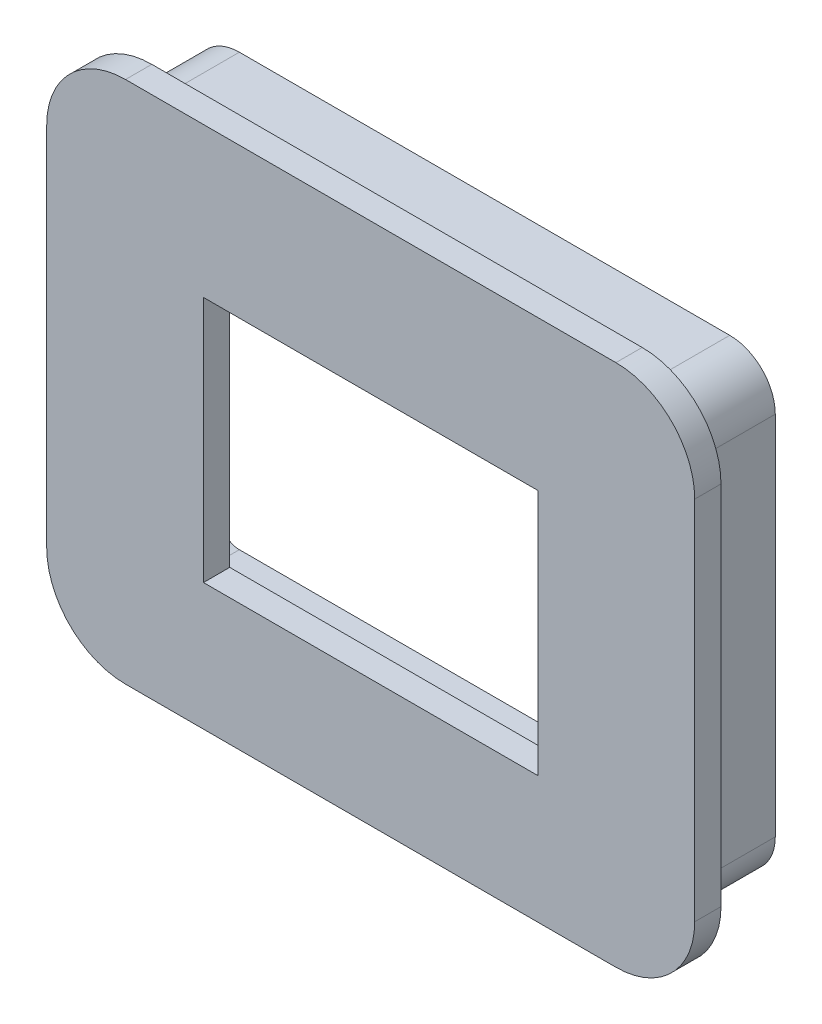
SolidWorks part; units mm, degrees
ref_plane "前视基准面" through (0, 0, 0) normal (0, 0, 1) x (1, 0, 0)
ref_plane "上视基准面" through (0, 0, 0) normal (0, 1, 0) x (1, 0, 0)
ref_plane "右视基准面" through (0, 0, 0) normal (1, 0, 0) x (0, 0, -1)
sketch "草图1" plane through (0, 0, 0) normal (0, 0, 1) x (1, 0, 0)
  line L4 (0, 22.9) -> (-28, 22.9)
  line L5 (-32.5, 18.4) -> (-32.5, -2.5)
  line L6 (-28, -7) -> (0, -7)
  line L7 (4.5, -2.5) -> (4.5, 18.4)
  line L8 (0, 22.9) -> (-28, 22.9)
  line L9 (-32.5, 18.4) -> (-32.5, -2.5)
  line L10 (-28, -7) -> (0, -7)
  line L11 (4.5, -2.5) -> (4.5, 18.4)
  arc A4 (4.5, 18.4) -> (0, 22.9) centre (0, 18.4) ccw
  arc A5 (-28, 22.9) -> (-32.5, 18.4) centre (-28, 18.4) ccw
  arc A6 (-32.5, -2.5) -> (-28, -7) centre (-28, -2.5) ccw
  arc A7 (0, -7) -> (4.5, -2.5) centre (0, -2.5) ccw
  arc A8 (4.5, 18.4) -> (0, 22.9) centre (0, 18.4) ccw
  arc A9 (-28, 22.9) -> (-32.5, 18.4) centre (-28, 18.4) ccw
  arc A10 (-32.5, -2.5) -> (-28, -7) centre (-28, -2.5) ccw
  arc A11 (0, -7) -> (4.5, -2.5) centre (0, -2.5) ccw
  dimension "D1" = 0
extrude "凸台-拉伸1" add sketch "草图1" along normal blind 1.5
sketch "草图3" plane through (0, 0, 0) normal (0, 0, 1) x (1, 0, 0)
  line L0 (-25.2327, 21) -> (-3.2178, 21)
  line L1 (-25.2327, 19.5) -> (-3.2178, 19.5)
  line L12 (-28, 19.5) -> (-25.2327, 19.5)
  line L13 (-25.2327, 19.5) -> (-25.2327, 21)
  line L14 (-25.2327, 21) -> (-28, 21)
  line L15 (-30.6, 18.4) -> (-30.6, -2.5)
  line L16 (-28, -5.1) -> (0, -5.1)
  line L17 (2.6, -2.5) -> (2.6, 18.4)
  line L18 (0, 21) -> (-3.2178, 21)
  line L19 (-3.2178, 21) -> (-3.2178, 19.5)
  line L20 (-3.2178, 19.5) -> (0, 19.5)
  line L21 (1.1, 18.4) -> (1.1, -2.5)
  line L22 (0, -3.6) -> (-28, -3.6)
  line L23 (-29.1, -2.5) -> (-29.1, 18.4)
  line L24 (-28, 19.5) -> (-25.2327, 19.5)
  line L26 (-25.2327, 21) -> (-28, 21)
  line L27 (-30.6, 18.4) -> (-30.6, -2.5)
  line L28 (-28, -5.1) -> (0, -5.1)
  line L29 (2.6, -2.5) -> (2.6, 18.4)
  line L30 (0, 21) -> (-3.2178, 21)
  line L32 (-3.2178, 19.5) -> (0, 19.5)
  line L33 (1.1, 18.4) -> (1.1, -2.5)
  line L34 (0, -3.6) -> (-28, -3.6)
  line L35 (-29.1, -2.5) -> (-29.1, 18.4)
  arc A8 (-28, 19.5) -> (-29.1, 18.4) centre (-28, 18.4) ccw
  arc A9 (-28, 21) -> (-30.6, 18.4) centre (-28, 18.4) ccw
  arc A10 (-30.6, -2.5) -> (-28, -5.1) centre (-28, -2.5) ccw
  arc A11 (0, -5.1) -> (2.6, -2.5) centre (0, -2.5) ccw
  arc A12 (2.6, 18.4) -> (0, 21) centre (0, 18.4) ccw
  arc A13 (1.1, 18.4) -> (0, 19.5) centre (0, 18.4) ccw
  arc A14 (0, -3.6) -> (1.1, -2.5) centre (0, -2.5) ccw
  arc A15 (-29.1, -2.5) -> (-28, -3.6) centre (-28, -2.5) ccw
  arc A16 (-28, 19.5) -> (-29.1, 18.4) centre (-28, 18.4) ccw
  arc A17 (-28, 21) -> (-30.6, 18.4) centre (-28, 18.4) ccw
  arc A18 (-30.6, -2.5) -> (-28, -5.1) centre (-28, -2.5) ccw
  arc A19 (0, -5.1) -> (2.6, -2.5) centre (0, -2.5) ccw
  arc A20 (2.6, 18.4) -> (0, 21) centre (0, 18.4) ccw
  arc A21 (1.1, 18.4) -> (0, 19.5) centre (0, 18.4) ccw
  arc A22 (0, -3.6) -> (1.1, -2.5) centre (0, -2.5) ccw
  arc A23 (-29.1, -2.5) -> (-28, -3.6) centre (-28, -2.5) ccw
  dimension "D1" = 0
extrude "凸台-拉伸2" add sketch "草图3" against normal blind 5 separate body
sketch "草图4" plane through (0, 0, 1.5) normal (0, 0, 1) x (1, 0, 0)
  line L8 (-4.45, 0.25) -> (-4.45, 14.35)
  line L9 (-23.55, 0.25) -> (-4.45, 0.25)
  line L10 (-23.55, 14.35) -> (-23.55, 0.25)
  line L11 (-4.45, 14.35) -> (-23.55, 14.35)
  line L12 (-4.45, 0.25) -> (-4.45, 14.35)
  line L13 (-23.55, 0.25) -> (-4.45, 0.25)
  line L14 (-23.55, 14.35) -> (-23.55, 0.25)
  line L15 (-4.45, 14.35) -> (-23.55, 14.35)
  dimension "D1" = 0.2
extrude "切除-拉伸1" cut sketch "草图4" against normal up to surface (1.5 mm away) up to face at (-14, 7.95, 0)
